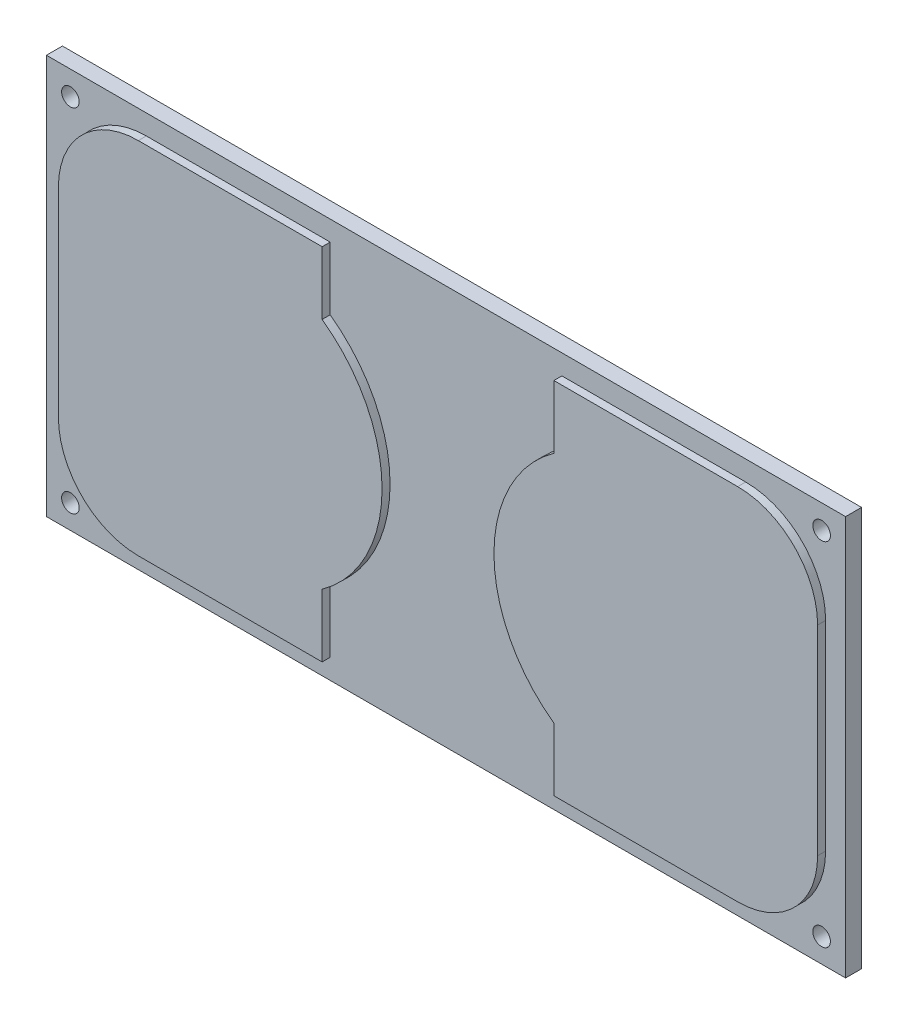
SolidWorks part; units mm, degrees
ref_plane "Plan de face" through (0, 0, 0) normal (0, 0, 1) x (1, 0, 0)
ref_plane "Plan de dessus" through (0, 0, 0) normal (0, 1, 0) x (1, 0, 0)
ref_plane "Plan de droite" through (0, 0, 0) normal (1, 0, 0) x (0, 0, -1)
sketch "Esquisse1" plane through (0, 0, 0) normal (0, 0, 1) x (1, 0, 0)
  line L0 (50, 50) -> (50, 0) construction
  line L1 (0, 0) -> (100, 0)
  line L2 (0, 0) -> (0, 50)
  line L3 (0, 50) -> (100, 50)
  line L4 (100, 0) -> (100, 50)
  line L5 (0, 25) -> (100, 25) construction
  circle A0 centre (3, 47) radius 1.1
  circle A1 centre (97, 47) radius 1.1
  circle A2 centre (3, 3) radius 1.1
  circle A3 centre (97, 3) radius 1.1
  dimension "D5" = 2.2
  dimension "D1" = 50
  dimension "D2" = 100
  dimension "D3" = 3
  dimension "D4" = 3
extrude "Boss.-Extru.1" add sketch "Esquisse1" along normal blind 2
sketch "Esquisse2" plane through (0, 0, 2) normal (0, 0, 1) x (1, 0, 0)
  line L0 (2.5, 37.5) -> (2.5, 12.5)
  line L1 (12.5, 2.5) -> (35.5, 2.5)
  line L2 (35.5, 2.5) -> (35.5, 10.3798)
  line L3 (35.5, 47.5) -> (12.5, 47.5)
  line L4 (0, 0) -> (100, 0) construction
  line L6 (0, 50) -> (0, 0) construction
  line L7 (100, 50) -> (0, 50) construction
  line L8 (35.5, 39.6202) -> (35.5, 47.5)
  line L9 (50, 50) -> (50, 0) construction
  line L10 (64.5, 39.6202) -> (64.5, 47.5)
  line L11 (64.5, 47.5) -> (87.5, 47.5)
  line L12 (64.5, 2.5) -> (64.5, 10.3798)
  line L13 (87.5, 2.5) -> (64.5, 2.5)
  line L14 (97.5, 37.5) -> (97.5, 12.5)
  arc A0 (2.5, 12.5) -> (12.5, 2.5) centre (12.5, 12.5) ccw
  arc A1 (2.5, 37.5) -> (12.5, 47.5) centre (12.5, 37.5) cw
  arc A2 (35.5, 39.6202) -> (35.5, 10.3798) centre (25, 25) cw
  arc A3 (64.5, 39.6202) -> (64.5, 10.3798) centre (75, 25) ccw
  arc A4 (97.5, 37.5) -> (87.5, 47.5) centre (87.5, 37.5) ccw
  arc A5 (97.5, 12.5) -> (87.5, 2.5) centre (87.5, 12.5) cw
  dimension "D5" = 10
  dimension "D6" = 18
  dimension "D7" = 25
  dimension "D1" = 45
  dimension "D2" = 33
  dimension "D3" = 2.5
  dimension "D4" = 2.5
  dimension "D8" = 25
extrude "Boss.-Extru.2" add sketch "Esquisse2" along normal blind 1
